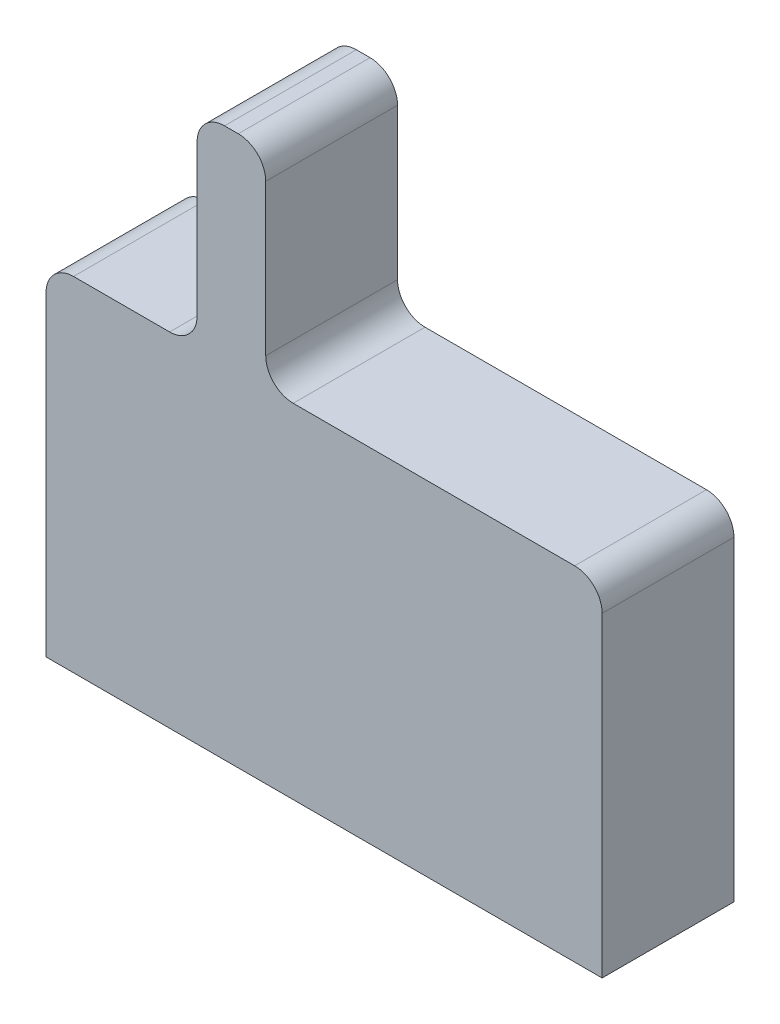
SolidWorks part; units mm, degrees
material "Pure Gold"
ref_plane "Front Plane" through (0, 0, 0) normal (0, 0, 1) x (1, 0, 0)
ref_plane "Top Plane" through (0, 0, 0) normal (0, 1, 0) x (1, 0, 0)
ref_plane "Right Plane" through (0, 0, 0) normal (1, 0, 0) x (0, 0, -1)
sketch "Sketch1" plane through (0, 0, 0) normal (0, 0, 1) x (1, 0, 0)
  line L0 (-0.925, 1.25) -> (-0.925, 2.75)
  line L1 (-2.025, 1.25) -> (-0.925, 1.25)
  line L2 (-2.025, 1.25) -> (-2.025, -1.25)
  line L3 (-2.025, -1.25) -> (2.025, -1.25)
  line L4 (2.025, 1.25) -> (2.025, -1.25)
  line L5 (-2.025, 1.25) -> (2.025, -1.25) construction
  line L6 (-2.025, -1.25) -> (2.025, 1.25) construction
  line L7 (-0.925, 2.75) -> (-0.425, 2.75)
  line L8 (-0.425, 2.75) -> (-0.425, 1.25)
  line L9 (-0.425, 1.25) -> (2.025, 1.25)
  point P0 (0, 0)
  point P8 (-0.675, 2.75)
  dimension "D1" = 4.05
  dimension "D2" = 2.5
  dimension "D3" = 1.35
  dimension "D4" = 4
  dimension "D5" = 0.5
extrude "Boss-Extrude1" add sketch "Sketch1" along normal blind 0.96
fillet "Fillet1" radius 0.2 6 edges at (-0.925, 1.25, 0.48) (-0.425, 1.25, 0.48) (-0.425, 2.75, 0.48) (-0.925, 2.75, 0.48) (2.025, 1.25, 0.48) (-2.025, 1.25, 0.48)
equation "\"D4@Sketch1\"=4mm"
